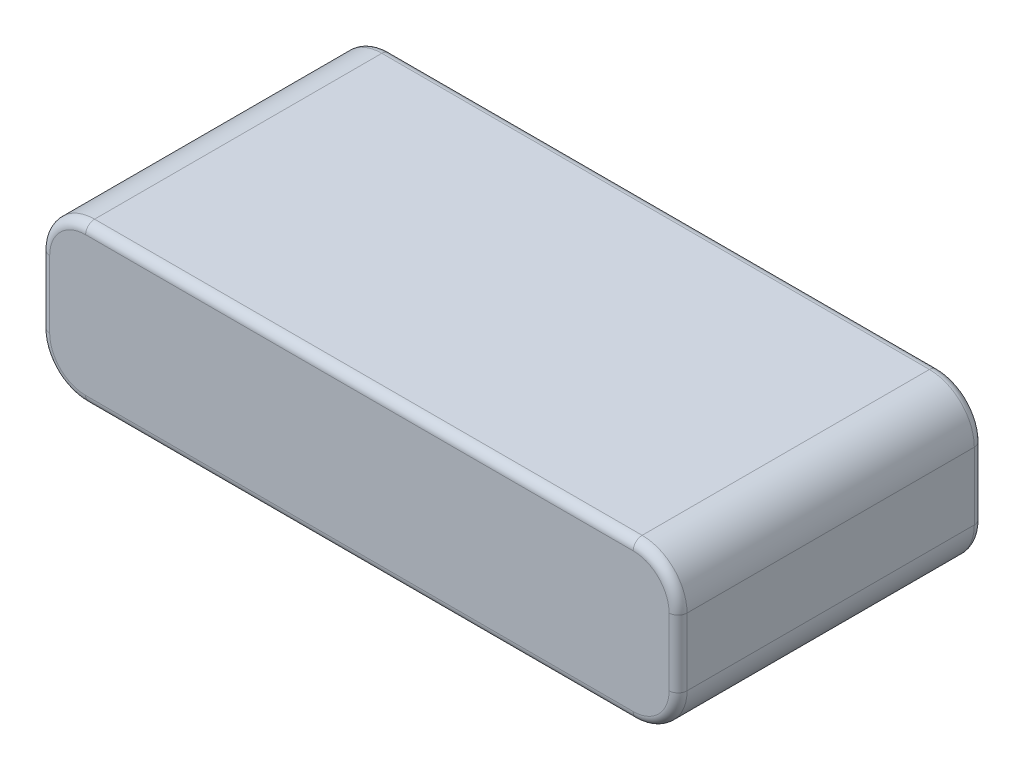
SolidWorks part; units mm, degrees
ref_plane "Front Plane" through (0, 0, 0) normal (0, 0, 1) x (1, 0, 0)
ref_plane "Top Plane" through (0, 0, 0) normal (0, 1, 0) x (1, 0, 0)
ref_plane "Right Plane" through (0, 0, 0) normal (1, 0, 0) x (0, 0, -1)
sketch "Sketch4" plane through (0, 0, 0) normal (0, 1, 0) x (1, 0, 0)
  line L1 (35.5, -17) -> (-35.5, -17)
  line L2 (35.5, -17) -> (35.5, 17)
  line L3 (35.5, 17) -> (-35.5, 17)
  line L4 (-35.5, -17) -> (-35.5, 17)
  line L5 (35.5, -17) -> (-35.5, 17) construction
  line L6 (35.5, 17) -> (-35.5, -17) construction
  point P0 (0, 0)
  dimension "D1" = 71
  dimension "D2" = 34
extrude "Boss-Extrude1" add sketch "Sketch4" along normal blind 17.5
fillet "Fillet1" radius 5 4 edges at (-35.5, 17.5, 0) (-35.5, 0, 0) (35.5, 0, 0) (35.5, 17.5, 0)
fillet "Fillet2" radius 1 16 edges at (34.0355, 16.0355, 17) (35.5, 8.75, 17) (34.0355, 1.4645, 17) (0, 0, 17) (-34.0355, 1.4645, 17) (-35.5, 8.75, 17) (-34.0355, 16.0355, 17) (0, 17.5, 17) (-34.0355, 1.4645, -17) (0, 0, -17) (34.0355, 1.4645, -17) (35.5, 8.75, -17) (34.0355, 16.0355, -17) (0, 17.5, -17) (-34.0355, 16.0355, -17) (-35.5, 8.75, -17)
sketch "Sketch6" plane through (0, 17.5, 0) normal (0, 1, 0) x (1, 0, 0)
  text T0 "<b>Battery</b>"
